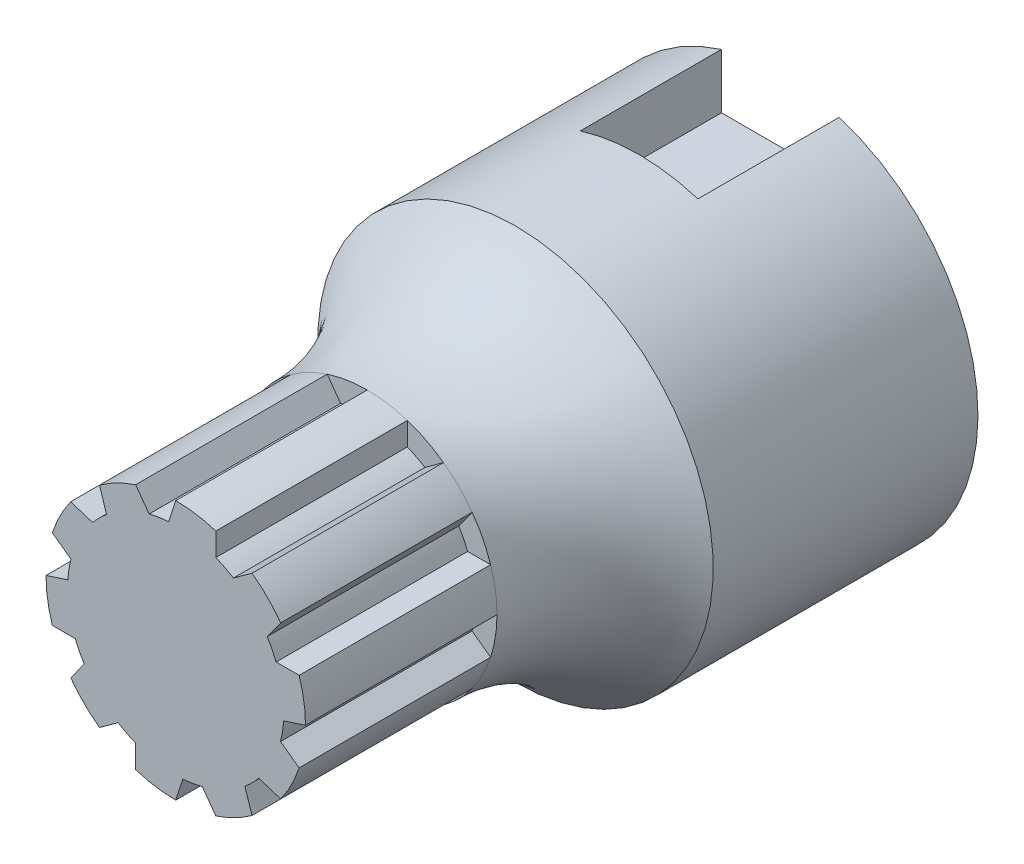
SolidWorks part; units mm, degrees
material "AISI 1045 Steel, cold drawn"
ref_plane "Front Plane" through (0, 0, 0) normal (0, 0, 1) x (1, 0, 0)
ref_plane "Top Plane" through (0, 0, 0) normal (0, 1, 0) x (1, 0, 0)
ref_plane "Right Plane" through (0, 0, 0) normal (1, 0, 0) x (0, 0, -1)
sketch "Sketch1" plane through (0, 0, 0) normal (0, 0, 1) x (1, 0, 0)
  line L0 (0, 10.5) -> (0, 0)
  line L1 (0, 0) -> (3.2447, 9.9861) construction
  line L2 (0, 0) -> (6.1717, 8.4947)
  line L3 (3.2447, 9.9861) -> (3.2447, 8.1262)
  line L4 (4.667, 7.4014) -> (6.1717, 8.4947)
  circle A0 centre (0, 0) radius 10.5 construction
  circle A1 centre (0, 0) radius 8.75 construction
  arc A2 (0, 10.5) -> (3.2447, 9.9861) centre (0, 0) cw
  arc A3 (6.1717, 8.4947) -> (3.2447, 9.9861) centre (0, 0) ccw construction
  arc A4 (3.2447, 8.1262) -> (4.667, 7.4014) centre (0, 0) cw
  dimension "D1" = 1.75
  dimension "D2" = 21
  dimension "D3" = 18
  dimension "D4" = 18
sketch "Sketch2" plane through (0, 0, 0) normal (1, 0, 0) x (0, 0, -1)
  line L0 (2.3551, 0) -> (2.3551, 8.6)
  line L1 (27.5, 16) -> (48.93, 16)
  line L2 (48.93, 16) -> (48.93, 0)
  line L3 (48.93, 0) -> (2.3551, 0)
  line L4 (0, 10.5) -> (15.5, 10.5) construction
  line L5 (2.3551, 8.6) -> (0, 8.6) construction
  line L6 (2.3551, 8.6) -> (15.5, 8.6)
  line L7 (15.5, 8.6) -> (15.5, 10.5)
  line L8 (42.58, 22.1477) -> (42.58, -4.3424) construction
  line L9 (0, 8.75) -> (0, -8.75) construction
  line L10 (37.5, 22.1477) -> (37.5, -4.3424) construction
  line L12 (48.93, 22.1477) -> (48.93, -4.3424) construction
  arc A0 (15.5, 10.5) -> (27.5, 16) centre (15.5, 26.3409) ccw
  dimension "D1" = 10
  dimension "D5" = 27.5
  dimension "D7" = 5.08
  dimension "D2" = 16
  dimension "D3" = 15.5
  dimension "D4" = 8.6
  dimension "D6" = 6.35
extrude "Boss-Extrude1" add sketch "Sketch1" against normal blind 20
pattern_circular "CirPattern1" count 10 over 360 about axis through (0, 0, 0) along (0, 0, 1) of "Boss-Extrude1"
revolve "Revolve1" add sketch "Sketch2" angle 360 about L3
sketch "Sketch3" plane through (0, 0, -48.93) normal (0, 0, -1) x (-1, 0, 0)
  line L0 (0, 0) -> (0, 16) construction
  line L1 (-4.7625, 16.4485) -> (4.7625, 16.4485)
  line L2 (-4.7625, 16.4485) -> (-4.7625, 10.8298)
  line L3 (-4.7625, 10.8298) -> (4.7625, 10.8298)
  line L4 (4.7625, 16.4485) -> (4.7625, 10.8298)
  line L5 (-4.7625, 15.2748) -> (4.7625, 15.2748) construction
  circle A0 centre (0, 0) radius 16 construction
  dimension "D1" = 9.525
  dimension "D2" = 4.445
extrude "Cut-Extrude1" cut sketch "Sketch3" against normal up to surface (11.43 mm away)
